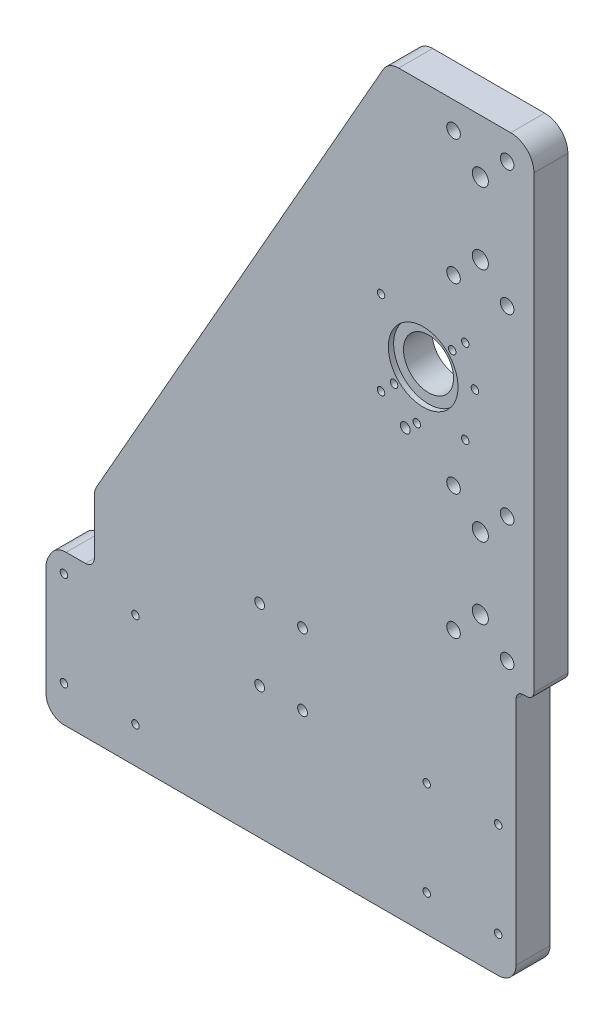
SolidWorks part; units mm, degrees
ref_plane "Front Plane" through (0, 0, 0) normal (0, 0, 1) x (1, 0, 0)
ref_plane "Top Plane" through (0, 0, 0) normal (0, 1, 0) x (1, 0, 0)
ref_plane "Right Plane" through (0, 0, 0) normal (1, 0, 0) x (0, 0, -1)
sketch "Sketch2" plane through (0, 0, 94) normal (0, 0, 1) x (1, 0, 0)
  line L1 (2186.978, 859.9095) -> (2457.8071, 859.9095)
  line L2 (2186.978, 859.9095) -> (2186.978, 457.9095)
  line L3 (2186.978, 457.9095) -> (2457.8071, 457.9095)
  line L4 (2457.8071, 859.9095) -> (2457.8071, 457.9095)
  line L6 (2441.9071, 859.9095) -> (2454.8071, 859.9095) construction
extrude "Boss-Extrude1" add sketch "Sketch2" along normal blind 19
sketch "Sketch3" plane through (0, 0, 113) normal (0, 0, 1) x (1, 0, 0)
  line L0 (2186.978, 859.9095) -> (2186.978, 457.9095) construction
  line L1 (2186.978, 864.5699) -> (2194.8071, 864.5699)
  line L2 (2186.978, 864.5699) -> (2186.978, 445.0092)
  line L3 (2186.978, 445.0092) -> (2194.8071, 445.0092)
  line L4 (2194.8071, 864.5699) -> (2194.8071, 445.0092)
extrude "Cut-Extrude1" cut sketch "Sketch3" against normal blind 20
sketch "Sketch4" plane through (0, 0, 113) normal (0, 0, 1) x (1, 0, 0)
  line L0 (2194.8071, 532.657) -> (2380.6092, 859.9095)
  line L1 (2194.8071, 457.9095) -> (2194.8071, 859.9095) construction
  line L2 (2457.8071, 859.9095) -> (2194.8071, 859.9095) construction
  line L3 (2380.6092, 859.9095) -> (2194.8071, 859.9095)
  line L4 (2194.8071, 859.9095) -> (2194.8071, 532.657)
extrude "Cut-Extrude2" cut sketch "Sketch4" against normal blind 20
fillet "Fillet1" radius 10 4 edges at (2457.8071, 457.9095, 103.5) (2194.8071, 457.9095, 103.5) (2194.8071, 532.657, 103.5) (2380.6092, 859.9095, 103.5)
hole_wizard "Tap Drill for M5 Tap1" positions "Sketch5" profile "Sketch6" hole size "M5" standard "ISO" end condition through all
sketch "Sketch5" plane through (0, 0, 113) normal (0, 0, 1) x (1, 0, 0)
  line L9 (2212.8071, 504.6607) -> (2439.8071, 504.6607) construction
  line L23 (2447.8071, 531.1607) -> (2407.8071, 531.1607) construction
  line L24 (2447.8071, 531.1607) -> (2447.8071, 478.1607) construction
  line L25 (2447.8071, 478.1607) -> (2407.8071, 478.1607) construction
  line L26 (2407.8071, 531.1607) -> (2407.8071, 478.1607) construction
  line L27 (2457.8071, 467.9095) -> (2457.8071, 859.9095) construction
  line L29 (2244.8071, 531.1607) -> (2204.8071, 531.1607) construction
  line L30 (2244.8071, 531.1607) -> (2244.8071, 478.1607) construction
  line L31 (2244.8071, 478.1607) -> (2204.8071, 478.1607) construction
  line L32 (2204.8071, 531.1607) -> (2204.8071, 478.1607) construction
  line L33 (2194.8071, 467.9095) -> (2194.8071, 530.0161) construction
  circle A2 centre (2407.8071, 531.1607) radius 2.5
  circle A3 centre (2447.8071, 531.1607) radius 2.5
  point P85 (2338.3071, 531.6607)
  point P87 (2314.3071, 531.6607)
  point P89 (2314.3071, 571.6607)
  point P91 (2338.3071, 571.6607)
  point P405 (2447.8071, 531.1607)
  point P408 (2447.8071, 478.1607)
  point P411 (2407.8071, 478.1607)
  point P414 (2407.8071, 531.1607)
  point P417 (2244.8071, 531.1607)
  point P420 (2244.8071, 478.1607)
  point P423 (2204.8071, 478.1607)
  point P426 (2204.8071, 531.1607)
  dimension "D7" = 5
  dimension "D10" = 5
  dimension "D4" = 53
  dimension "D5" = 40
  dimension "D6" = 26.5
  dimension "D11" = 50
  dimension "D12" = 40
  dimension "D13" = 53
  dimension "D15" = 50
sketch "Sketch6" plane through (2338.3071, 531.6607, 113) normal (1, 0, 0) x (0, -1, 0)
  line L0 (0, 0) -> (0, 19)
  line L1 (0, 19) -> (2.1, 19)
  line L2 (2.1, 19) -> (2.1, 0)
  line L5 (2.1, 0) -> (0, 0)
  line L11 (0, -6.35) -> (0, 107.95) construction
  dimension "Thru Hole Dia." = 4.2
  dimension "Thru Hole Depth" = 19
fillet "Fillet2" radius 3 1 edges at (2457.8071, 859.9095, 103.5)
hole_wizard "M7 Clearance Hole1" positions "Sketch7" profile "Sketch8" hole size "M7" standard "ISO" end condition through all
sketch "Sketch7" plane through (0, 0, 113) normal (0, 0, 1) x (1, 0, 0)
  point P0 (2422.8071, 612.9095)
  point P2 (2437.8071, 627.9095)
  point P4 (2452.8071, 612.9095)
  point P6 (2452.8071, 682.9095)
  point P8 (2437.8071, 667.9095)
  point P10 (2422.8071, 682.9095)
  point P12 (2452.8071, 784.9095)
  point P14 (2422.8071, 854.9095)
  point P16 (2452.8071, 854.9095)
  point P18 (2422.8071, 784.9095)
  point P20 (2437.8071, 799.9095)
  point P22 (2437.8071, 839.9095)
sketch "Sketch8" plane through (2422.8071, 612.9095, 113) normal (1, 0, 0) x (0, -1, 0)
  line L0 (0, 0) -> (0, 19)
  line L1 (0, 19) -> (3.8, 19)
  line L2 (3.8, 19) -> (3.8, 0)
  line L5 (3.8, 0) -> (0, 0)
  line L11 (0, -6.35) -> (0, 107.95) construction
  dimension "Thru Hole Dia." = 7.6
  dimension "Thru Hole Depth" = 19
hole_wizard "M5 Clearance Hole3" positions "Sketch9" profile "Sketch10" hole size "M5" standard "ISO"
sketch "Sketch9" plane through (0, 0, 94) normal (0, 0, -1) x (-1, 0, 0)
  point P0 (-2428.8071, 731.9095)
  point P2 (-2428.8071, 713.9095)
  point P4 (-2382.8071, 713.9095)
  point P6 (-2382.8071, 731.9095)
sketch "Sketch10" plane through (2428.8071, 731.9095, 94) normal (1, 0, 0) x (0, 1, 0)
  line L0 (0, 0) -> (0, 19)
  line L1 (0, 19) -> (2.75, 19)
  line L2 (2.75, 19) -> (2.75, 0)
  line L5 (2.75, 0) -> (0, 0)
  line L11 (0, -6.35) -> (0, 107.95) construction
  dimension "Thru Hole Dia." = 5.5
  dimension "Thru Hole Depth" = 19
sketch "Sketch11" plane through (0, 0, 113) normal (0, 0, 1) x (1, 0, 0)
  circle A3 centre (2405.8071, 731.9095) radius 19.5
  dimension "D1" = 19.5
extrude "Cut-Extrude4" cut sketch "Sketch11" against normal blind 32.2668
sketch "Sketch12" plane through (0, 0, 113) normal (0, 0, 1) x (1, 0, 0)
  line L10 (2221.8071, 542.1607) -> (2189.7804, 542.1607)
  line L11 (2221.8071, 583.4258) -> (2221.8071, 542.1607)
  line L12 (2221.8071, 583.4258) -> (2189.7804, 542.1607)
extrude "Cut-Extrude5" cut sketch "Sketch12" against normal blind 20
fillet "Fillet3" radius 10 2 edges at (2221.8071, 580.212, 103.5) (2200.203, 542.1607, 103.5)
fillet "Fillet4" radius 5 1 edges at (2221.8071, 542.1607, 103.5)
hole_wizard "Tap Drill for M5 Tap2" positions "Sketch13" profile "Sketch14" hole size "M5" standard "ISO" end condition through all
sketch "Sketch13" plane through (0, 0, 94) normal (0, 0, -1) x (-1, 0, 0)
  point P0 (-2429.3771, 755.4795)
  point P2 (-2382.2371, 755.4795)
  point P4 (-2429.3771, 708.3395)
  point P6 (-2382.2371, 708.3395)
sketch "Sketch14" plane through (2429.3771, 755.4795, 94) normal (1, 0, 0) x (0, 1, 0)
  line L0 (0, 0) -> (0, 19)
  line L1 (0, 19) -> (2.1, 19)
  line L2 (2.1, 19) -> (2.1, 0)
  line L5 (2.1, 0) -> (0, 0)
  line L11 (0, -6.35) -> (0, 107.95) construction
  dimension "Thru Hole Dia." = 4.2
  dimension "Thru Hole Depth" = 19
sketch "Sketch15" plane through (0, 0, 113) normal (0, 0, 1) x (1, 0, 0)
  line L0 (2457.8071, 467.9095) -> (2457.8071, 856.9095) construction
  line L1 (2454.8071, 859.9095) -> (2386.431, 859.9095) construction
  line L2 (2457.8071, 597.1048) -> (2457.8071, 856.9095)
  line L3 (2454.8071, 859.9095) -> (2386.431, 859.9095)
  line L4 (2467.8071, 605.1048) -> (2467.8071, 856.9095)
  line L5 (2454.8071, 869.9095) -> (2392.1086, 869.9095)
  line L6 (2463.8071, 601.1048) -> (2461.8071, 601.1048)
  line L7 (2223.111, 582.5085) -> (2377.7348, 854.8469) construction
  line L8 (2377.7348, 854.8469) -> (2383.4125, 864.8469)
  line L9 (2467.8071, 467.9095) -> (2467.8071, 856.9095) construction
  line L10 (2457.8071, 467.9095) -> (2457.8071, 856.9095) construction
  line L11 (2454.8071, 869.9095) -> (2386.431, 869.9095) construction
  line L12 (2457.8071, 597.1048) -> (2457.8071, 582.296)
  arc A0 (2386.431, 859.9095) -> (2377.7348, 854.8469) centre (2386.431, 849.9095) ccw construction
  arc A1 (2457.8071, 856.9095) -> (2454.8071, 859.9095) centre (2454.8071, 856.9095) ccw construction
  arc A2 (2386.431, 859.9095) -> (2377.7348, 854.8469) centre (2386.431, 849.9095) ccw
  arc A3 (2457.8071, 856.9095) -> (2454.8071, 859.9095) centre (2454.8071, 856.9095) ccw
  arc A4 (2467.8071, 856.9095) -> (2454.8071, 869.9095) centre (2454.8071, 856.9095) ccw
  arc A5 (2463.8071, 601.1048) -> (2467.8071, 605.1048) centre (2463.8071, 605.1048) ccw
  arc A6 (2386.431, 869.9095) -> (2369.0387, 859.7842) centre (2386.431, 849.9095) ccw construction
  arc A7 (2457.8071, 597.1048) -> (2461.8071, 601.1048) centre (2461.8071, 597.1048) cw
  arc A8 (2383.4125, 864.8469) -> (2392.1086, 869.9095) centre (2392.1086, 859.9095) cw
  line M54 (2457.8071, 467.9095) -> (2457.8071, 856.9095)
  arc M55 (2457.8071, 856.9095) -> (2454.8071, 859.9095) centre (2454.8071, 856.9095) ccw
  line M56 (2454.8071, 859.9095) -> (2386.431, 859.9095)
  arc M57 (2386.431, 859.9095) -> (2377.7348, 854.8469) centre (2386.431, 849.9095) ccw
  dimension "D2" = 4
  dimension "D3" = 10
  dimension "D1" = 10
extrude "Boss-Extrude2" add sketch "Sketch15" against normal up to surface (19 mm away) contours A8 L8 A7 L6 A5 L4 A4 L5 M57 M56 M55 M54 up to face at (2427.2771, 755.4795, 94)
sketch "Sketch16" plane through (0, 0, 94) normal (0, 0, -1) x (-1, 0, 0)
  circle A0 centre (-2405.8071, 731.9095) radius 19.5 construction
  circle A1 centre (-2405.8071, 731.9095) radius 19.5
  circle A5 centre (-2405.8071, 731.9095) radius 14
extrude "Boss-Extrude3" add sketch "Sketch16" against normal offset from surface (16 mm away) 3 contours A1 | A5 up to face at (2326.7058, 605.5646, 113)
hole_wizard "M5 Clearance Hole4" positions "Sketch17" profile "Sketch18" hole size "M5" standard "ISO" end condition through all
sketch "Sketch17" plane through (0, 0, 94) normal (0, 0, -1) x (-1, 0, 0)
  line L1 (-2375.8071, 687.9095) -> (-2375.8071, 706.9095) construction
  point P0 (-2395.8071, 697.4095)
  dimension "D1" = 20
sketch "Sketch18" plane through (2395.8071, 697.4095, 94) normal (1, 0, 0) x (0, 1, 0)
  line L0 (0, 0) -> (0, 19)
  line L1 (0, 19) -> (2.75, 19)
  line L2 (2.75, 19) -> (2.75, 0)
  line L5 (2.75, 0) -> (0, 0)
  line L11 (0, -6.35) -> (0, 107.95) construction
  dimension "Thru Hole Dia." = 5.5
  dimension "Thru Hole Depth" = 19
hole_wizard "M5 Clearance Hole5" positions "Sketch19" profile "Sketch20" hole size "M5" standard "ISO" end condition through all
sketch "Sketch19" plane through (0, 0, 94) normal (0, 0, -1) x (-1, 0, 0)
  point P0 (-2338.3071, 531.6607)
  point P3 (-2314.3071, 531.6607)
  point P6 (-2314.3071, 571.6607)
  point P9 (-2338.3071, 571.6607)
sketch "Sketch20" plane through (2338.3071, 531.6607, 94) normal (1, 0, 0) x (0, 1, 0)
  line L0 (0, 0) -> (0, 19)
  line L1 (0, 19) -> (2.75, 19)
  line L2 (2.75, 19) -> (2.75, 0)
  line L5 (2.75, 0) -> (0, 0)
  line L11 (0, -6.35) -> (0, 107.95) construction
  dimension "Thru Hole Dia." = 5.5
  dimension "Thru Hole Depth" = 19
hole_wizard "M8 Clearance Hole1" positions "Sketch21" profile "Sketch22" hole size "M8" standard "ISO" end condition through all
sketch "Sketch21" plane through (0, 0, 94) normal (0, 0, -1) x (-1, 0, 0)
  point P2 (-2437.8071, 627.9095)
  point P5 (-2437.8071, 667.9095)
  point P8 (-2437.8071, 799.9095)
  point P11 (-2437.8071, 839.9095)
sketch "Sketch22" plane through (2437.8071, 627.9095, 94) normal (1, 0, 0) x (0, 1, 0)
  line L0 (0, 0) -> (0, 19)
  line L1 (0, 19) -> (4.5, 19)
  line L2 (4.5, 19) -> (4.5, 0)
  line L5 (4.5, 0) -> (0, 0)
  line L11 (0, -6.35) -> (0, 107.95) construction
  dimension "Thru Hole Dia." = 9
  dimension "Thru Hole Depth" = 19
hole_wizard "Tap Drill for M5 Tap3" positions "Sketch23" profile "Sketch24" hole size "M5" standard "ISO" end condition through all
sketch "Sketch23" plane through (0, 0, 94) normal (0, 0, -1) x (-1, 0, 0)
  point P0 (-2422.0706, 748.173)
  point P2 (-2434.7985, 735.4451)
  point P4 (-2402.2716, 702.9181)
  point P6 (-2389.5437, 715.6461)
sketch "Sketch24" plane through (2422.0706, 748.173, 94) normal (1, 0, 0) x (0, 1, 0)
  line L0 (0, 0) -> (0, 19)
  line L1 (0, 19) -> (2.1, 19)
  line L2 (2.1, 19) -> (2.1, 0)
  line L5 (2.1, 0) -> (0, 0)
  line L11 (0, -6.35) -> (0, 107.95) construction
  dimension "Thru Hole Dia." = 4.2
  dimension "Thru Hole Depth" = 19
sketch "Sketch25" plane through (0, 0, 94) normal (0, 0, -1) x (-1, 0, 0)
  line L1 (-2430.2086, 735.4451) -> (-2432.5035, 739.4201)
  line L2 (-2432.5035, 739.4201) -> (-2437.0935, 739.4201)
  line L3 (-2437.0935, 739.4201) -> (-2439.3884, 735.4451)
  line L4 (-2439.3884, 735.4451) -> (-2437.0935, 731.4701)
  line L5 (-2437.0935, 731.4701) -> (-2432.5035, 731.4701)
  line L6 (-2432.5035, 731.4701) -> (-2430.2086, 735.4451)
  line L7 (-2426.6605, 748.173) -> (-2424.3655, 744.198)
  line L8 (-2424.3655, 744.198) -> (-2419.7756, 744.198)
  line L9 (-2419.7756, 744.198) -> (-2417.4806, 748.173)
  line L10 (-2417.4806, 748.173) -> (-2419.7756, 752.148)
  line L11 (-2419.7756, 752.148) -> (-2424.3655, 752.148)
  line L12 (-2424.3655, 752.148) -> (-2426.6605, 748.173)
  line L13 (-2402.2716, 707.5081) -> (-2406.2466, 705.2131)
  line L14 (-2406.2466, 705.2131) -> (-2406.2466, 700.6232)
  line L15 (-2406.2466, 700.6232) -> (-2402.2716, 698.3282)
  line L16 (-2402.2716, 698.3282) -> (-2398.2966, 700.6232)
  line L17 (-2398.2966, 700.6232) -> (-2398.2966, 705.2131)
  line L18 (-2398.2966, 705.2131) -> (-2402.2716, 707.5081)
  line L19 (-2389.5437, 720.236) -> (-2393.5187, 717.941)
  line L20 (-2393.5187, 717.941) -> (-2393.5187, 713.3511)
  line L21 (-2393.5187, 713.3511) -> (-2389.5437, 711.0561)
  line L22 (-2389.5437, 711.0561) -> (-2385.5687, 713.3511)
  line L23 (-2385.5687, 713.3511) -> (-2385.5687, 717.941)
  line L24 (-2385.5687, 717.941) -> (-2389.5437, 720.236)
  circle A0 centre (-2434.7985, 735.4451) radius 3.975 construction
  circle A1 centre (-2422.0706, 748.173) radius 3.975 construction
  circle A2 centre (-2402.2716, 702.9181) radius 3.975 construction
  circle A3 centre (-2389.5437, 715.6461) radius 3.975 construction
  dimension "D1" = 7.95
  dimension "D2" = 7.95
  dimension "D3" = 7.95
  dimension "D4" = 7.95
extrude "Cut-Extrude6" cut sketch "Sketch25" against normal blind 4
equation "\"D12@Sketch5\"=\"D5@Sketch5\""
equation "\"D2@Sketch25\"=\"D1@Sketch25\""
equation "\"D3@Sketch25\"=\"D1@Sketch25\""
equation "\"D4@Sketch25\"=\"D1@Sketch25\""
